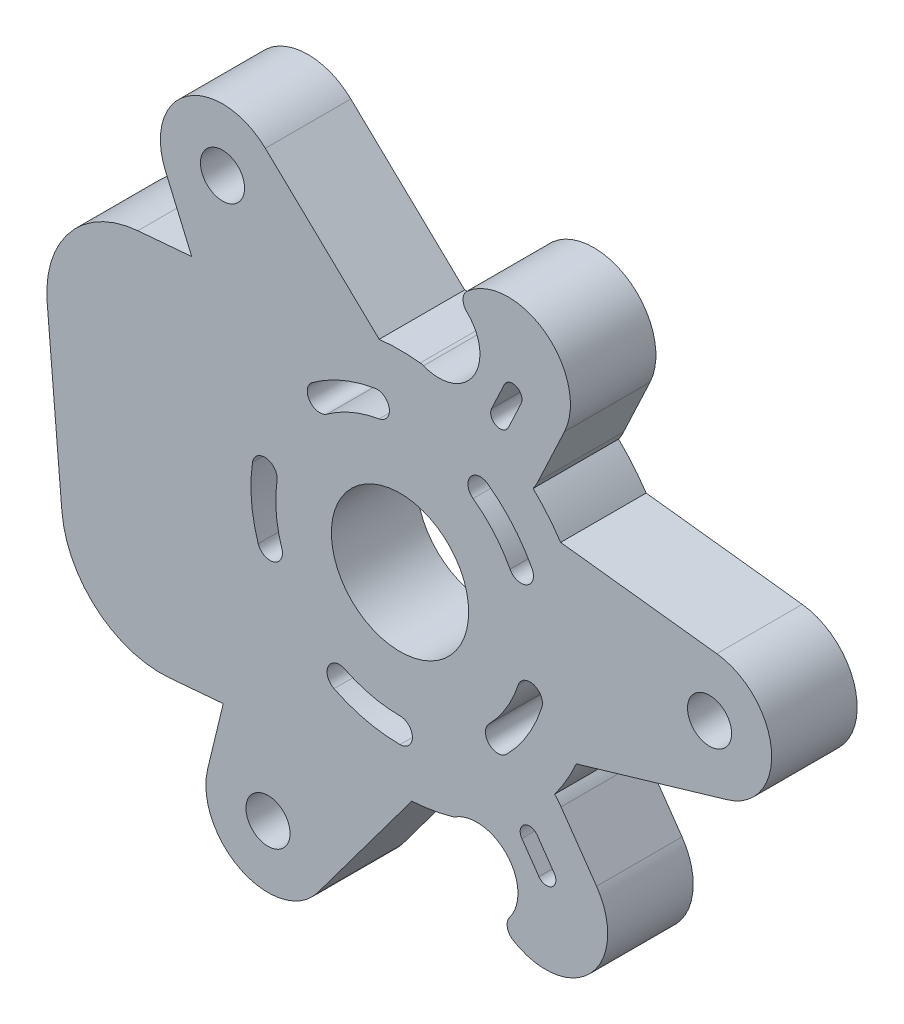
SolidWorks part; units mm, degrees
ref_plane "Front Plane" through (0, 0, 0) normal (0, 0, 1) x (1, 0, 0)
ref_plane "Top Plane" through (0, 0, 0) normal (0, 1, 0) x (1, 0, 0)
ref_plane "Right Plane" through (0, 0, 0) normal (1, 0, 0) x (0, 0, -1)
sketch "Sketch1" plane through (0, 0, 0) normal (0, 0, 1) x (1, 0, 0)
  circle A0 centre (0, 0) radius 30
  dimension "D1" = 60
extrude "Boss-Extrude1" add sketch "Sketch1" along normal blind 6.88
sketch "Sketch2" plane through (0, 0, 6.88) normal (0, 0, 1) x (1, 0, 0)
  line L0 (-15.4842, -21.4532) -> (-9.7191, 2.3536)
  line L1 (-10.6246, -22.63) -> (0, 0) construction
  line L2 (-6.6151, -25.6172) -> (8.0191, -5.9744)
  line L3 (-18.8776, 18.5374) -> (-9.1835, -3.9576)
  line L4 (-10.8369, 24.1363) -> (6.8978, 7.2402)
  line L5 (25.4927, 7.0798) -> (1.1644, 9.932)
  line L6 (26.3211, -2.6831) -> (2.8213, -9.5938)
  circle A0 centre (0, 0) radius 25 construction
  circle A1 centre (-14.2858, 20.5162) radius 1.775
  circle A2 centre (24.9105, 2.1138) radius 1.775
  circle A3 centre (-10.6246, -22.63) radius 1.775
  circle A4 centre (-10.6246, -22.63) radius 5
  circle A5 centre (-14.2858, 20.5162) radius 5
  circle A6 centre (24.9105, 2.1138) radius 5
  circle A7 centre (0, 0) radius 10
  circle A8 centre (0, 0) radius 30 construction
  point P32 (0, 0)
  circle M1 centre (0, 0) radius 30
  dimension "D1" = 50
  dimension "D2" = 3.55
  dimension "D3" = 20
  dimension "D4" = 3
extrude "Cut-Extrude1" cut sketch "Sketch2" against normal through all contours A5 A4 L0 L3 M1 | A6 A5 L4 L5 M1 | A6 L6 L2 A4 M1 | A3 | A2 | A1
sketch "Sketch3" plane through (0, 0, 6.88) normal (0, 0, 1) x (1, 0, 0)
  circle A0 centre (0, 0) radius 5.525
  dimension "D1" = 11.05
extrude "Cut-Extrude2" cut sketch "Sketch3" against normal through all
sketch "Sketch4" plane through (0, 0, 6.88) normal (0, 0, 1) x (1, 0, 0)
  circle A0 centre (0, 0) radius 15.5
  circle A1 centre (0, 0) radius 5.525
  dimension "D1" = 31
extrude "Boss-Extrude2" add sketch "Sketch4" against normal up to vertex (6.88 mm away)
sketch "Sketch6" plane through (0, 0, 6.88) normal (0, 0, 1) x (1, 0, 0)
  line L0 (-5.1594, 14.6161) -> (-29.0735, 12.5869)
  line L1 (-29.0735, 12.5869) -> (-26.5369, -17.3057)
  line L2 (-26.5369, -17.3057) -> (-2.6229, -15.2765)
  line L3 (-27.8052, -2.3594) -> (0, 0) construction
  line L4 (0, 0) -> (24.9105, 2.1138) construction
  arc A0 (-13.8704, 6.9182) -> (-12.5064, -9.1564) centre (0, 0) ccw construction
  arc A1 (-5.1594, 14.6161) -> (-2.6229, -15.2765) centre (0, 0) ccw
  dimension "D1" = 24
  dimension "D2" = 30
extrude "Boss-Extrude3" add sketch "Sketch6" against normal blind 6.88
fillet "Fillet1" radius 8 2 edges at (-29.0735, 12.5869, 3.44) (-26.5369, -17.3057, 3.44)
sketch "Sketch7" plane through (0, 0, 6.88) normal (0, 0, 1) x (1, 0, 0)
  line L0 (0, 0) -> (6.5873, 14.0306) construction
  line L1 (6.5873, 14.0306) -> (8.7122, 18.5566) construction
  line L2 (8.7122, 18.5566) -> (6.5873, 14.0306) construction
  line L3 (13.2382, 16.4317) -> (11.1133, 11.9057)
  line L4 (4.1862, 20.6815) -> (2.0613, 16.1555)
  line L5 (0, 0) -> (29.8926, 2.5365) construction
  line L6 (11.7144, -16.8233) -> (8.8572, -12.7201) construction
  line L7 (15.8176, -13.9661) -> (12.9605, -9.8629)
  line L8 (7.6111, -19.6805) -> (4.754, -15.5772)
  arc A0 (12.9266, 8.553) -> (-1.6765, 15.4091) centre (0, 0) ccw construction
  arc A1 (13.2382, 16.4317) -> (4.1862, 20.6815) centre (8.7122, 18.5566) ccw
  arc A2 (2.0613, 16.1555) -> (11.1133, 11.9057) centre (6.5873, 14.0306) ccw
  arc A3 (26.3211, -2.6831) -> (25.4927, 7.0798) centre (24.9105, 2.1138) ccw construction
  arc A4 (15.8176, -13.9661) -> (7.6111, -19.6805) centre (11.7144, -16.8233) cw
  arc A5 (4.754, -15.5772) -> (12.9605, -9.8629) centre (8.8572, -12.7201) cw
  point P6 (7.6497, 16.2936)
  point P18 (10.2858, -14.7717)
  dimension "D1" = 5
  dimension "D2" = 5
extrude "Boss-Extrude4" add sketch "Sketch7" against normal up to vertex (6.88 mm away)
sketch "Sketch8" plane through (0, 0, 6.88) normal (0, 0, 1) x (1, 0, 0)
  line L0 (11.1133, 11.9057) -> (13.2382, 16.4317) construction
  line L1 (0, 0) -> (10.8371, 23.0826) construction
  line L2 (0, 0) -> (29.8926, 2.5365) construction
  line L3 (10.4207, -13.2154) -> (11.7922, -15.1851) construction
  line L4 (11.0362, -12.7869) -> (12.4077, -14.7565)
  line L5 (12.1757, 14.1687) -> (3.1237, 18.4185) construction
  line L6 (8.0449, 14.7823) -> (9.0649, 16.9549) construction
  line L7 (8.7238, 14.4636) -> (9.7438, 16.6361)
  line L8 (7.366, 15.1011) -> (8.386, 17.2736)
  line L9 (9.8052, -13.644) -> (11.1767, -15.6136)
  line L10 (4.1862, 20.6815) -> (2.0613, 16.1555) construction
  arc A0 (26.3211, -2.6831) -> (25.4927, 7.0798) centre (24.9105, 2.1138) ccw construction
  arc A1 (11.0362, -12.7869) -> (9.8052, -13.644) centre (10.4207, -13.2154) ccw
  arc A2 (11.1767, -15.6136) -> (12.4077, -14.7565) centre (11.7922, -15.1851) ccw
  circle A3 centre (6.1826, -17.6288) radius 3.3071
  arc A4 (13.2382, 16.4317) -> (4.1862, 20.6815) centre (8.7122, 18.5566) ccw construction
  arc A5 (8.7238, 14.4636) -> (7.366, 15.1011) centre (8.0449, 14.7823) cw
  arc A6 (8.386, 17.2736) -> (9.7438, 16.6361) centre (9.0649, 16.9549) cw
  circle A7 centre (3.1237, 18.4185) radius 3.3071
  point P14 (11.1064, -14.2002)
  point P22 (8.5549, 15.8686)
  dimension "D1" = 6.6142
  dimension "D2" = 2.4001
  dimension "D4" = 0.75
  dimension "D3" = 6
extrude "Cut-Extrude3" cut sketch "Sketch8" against normal through all
fillet "Fillet2" radius 1 4 edges at (1.7778, 15.3977, 3.44) (4.5882, 21.3837, 3.44) (8.1257, -20.3049, 3.44) (4.3469, -14.878, 3.44)
sketch "Sketch10" plane through (0, 0, 6.88) normal (0, 0, 1) x (1, 0, 0)
  line L0 (0, 0) -> (-27.8052, -2.3594) construction
  line L1 (-28.3971, 4.6155) -> (-27.2133, -9.3343) construction
  arc A0 (-10.4624, -3.3968) -> (-10.8852, 1.5853) centre (0, 0) cw construction
  arc A1 (-11.8747, 1.7294) -> (-11.4135, -3.7056) centre (0, 0) ccw
  arc A2 (-9.8956, 1.4412) -> (-9.5113, -3.088) centre (0, 0) ccw
  arc A3 (-9.8956, 1.4412) -> (-11.8747, 1.7294) centre (-10.8852, 1.5853) ccw
  arc A4 (-11.4135, -3.7056) -> (-9.5113, -3.088) centre (-10.4624, -3.3968) ccw
  circle A5 centre (0, 0) radius 5.525 construction
  point P3 (-10.9606, -0.9301)
  dimension "D1" = 10
  dimension "D2" = 1
  dimension "D3" = 5
extrude "Cut-Extrude4" cut sketch "Sketch10" against normal through all
pattern_circular "CirPattern7" count 5 over 360 about axis through (0, 0, 0) along (0, 0, 1) of "Cut-Extrude4"
